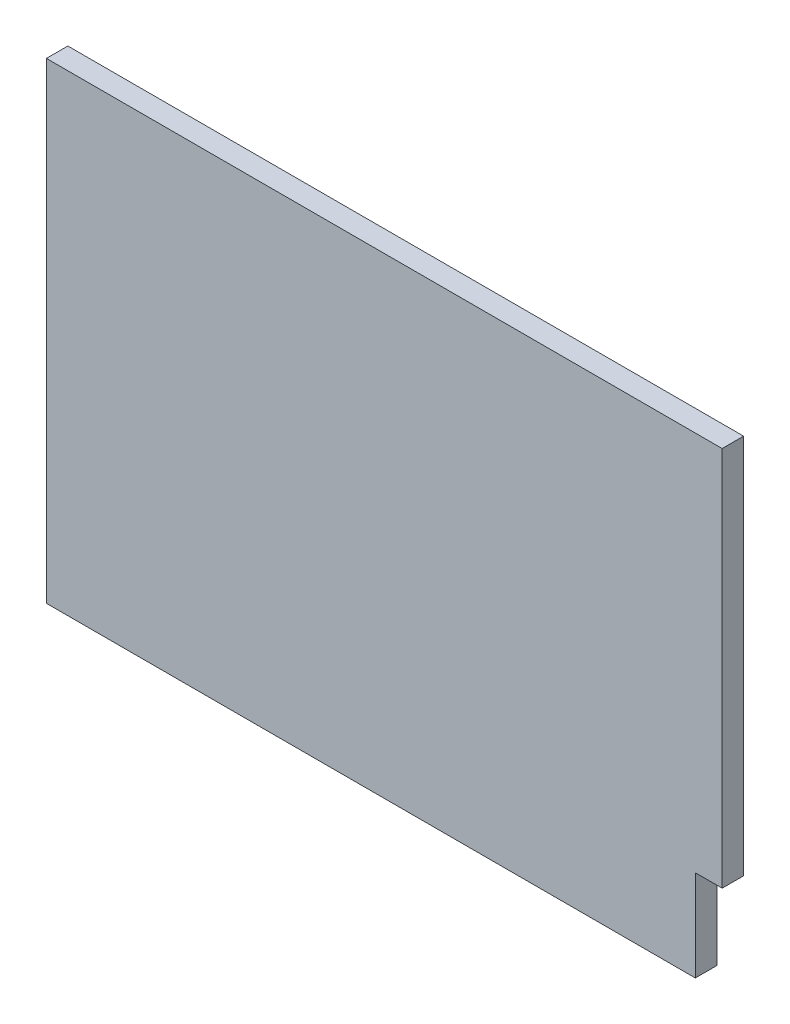
SolidWorks part; units mm, degrees
material "Acrylic (Medium-high impact)"
ref_plane "Front Plane" through (0, 0, 0) normal (0, 0, 1) x (1, 0, 0)
ref_plane "Top Plane" through (0, 0, 0) normal (0, 1, 0) x (1, 0, 0)
ref_plane "Right Plane" through (0, 0, 0) normal (1, 0, 0) x (0, 0, -1)
sketch "Sketch1" plane through (0, 0, 0) normal (0, 0, 1) x (1, 0, 0)
  line L0 (315, -135) -> (290, -135)
  line L1 (-315, 220) -> (315, 220)
  line L2 (-315, 220) -> (-315, -220)
  line L3 (-315, -220) -> (290, -220)
  line L4 (315, 220) -> (315, -135)
  line L5 (-315, 220) -> (290, -202.5397) construction
  line L6 (-315, -220) -> (315, 220) construction
  line L7 (290, -135) -> (290, -220)
  point P0 (0, 0)
  dimension "D1" = 440
  dimension "D2" = 630
  dimension "D3" = 355
  dimension "D4" = 25
extrude "Boss-Extrude1" add sketch "Sketch1" along normal blind 20
